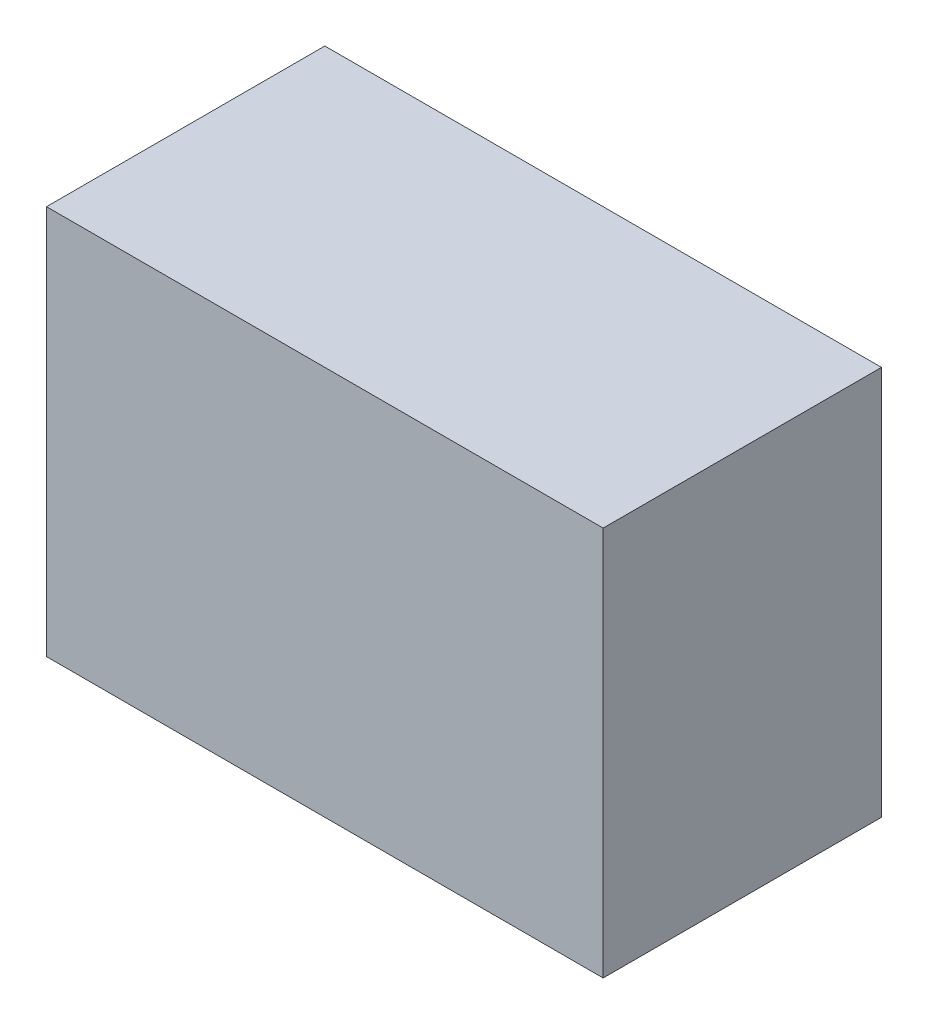
SolidWorks part; units mm, degrees
ref_plane "前视基准面" through (0, 0, 0) normal (0, 0, 1) x (1, 0, 0)
ref_plane "上视基准面" through (0, 0, 0) normal (0, 1, 0) x (1, 0, 0)
ref_plane "右视基准面" through (0, 0, 0) normal (1, 0, 0) x (0, 0, -1)
sketch "草图2" plane through (0, 0, 0) normal (0, 0, 1) x (1, 0, 0)
  line L1 (-500, 350) -> (500, 350)
  line L2 (-500, 350) -> (-500, -350)
  line L3 (-500, -350) -> (500, -350)
  line L4 (500, 350) -> (500, -350)
  line L5 (-500, 350) -> (500, -350) construction
  line L6 (-500, -350) -> (500, 350) construction
  point P0 (0, 0)
extrude "拉伸1" add sketch "草图2" along normal blind 500
shell "抽壳1" thickness 3
